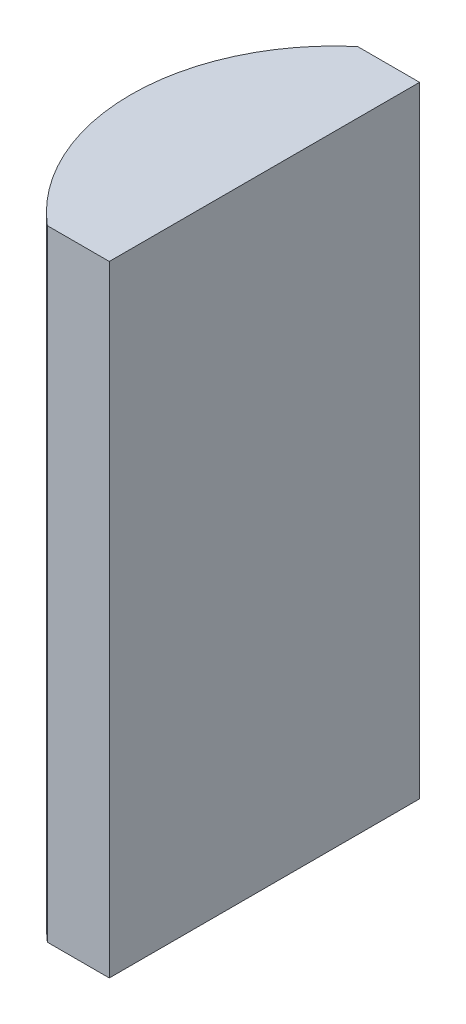
SolidWorks part; units mm, degrees
ref_plane "前视基准面" through (0, 0, 0) normal (0, 0, 1) x (1, 0, 0)
ref_plane "上视基准面" through (0, 0, 0) normal (0, 1, 0) x (1, 0, 0)
ref_plane "右视基准面" through (0, 0, 0) normal (1, 0, 0) x (0, 0, -1)
sketch "草图1" plane through (0, 0, 0) normal (0, 1, 0) x (1, 0, 0)
  line L0 (10.7432, 0) -> (-19.1624, 0) construction
  line L1 (0.1086, 5) -> (2.1052, 5)
  line L2 (0.1086, -5) -> (2.1052, -5)
  line L3 (2.1052, 5) -> (2.1052, -5)
  arc A0 (0.1086, 5) -> (0.1086, -5) centre (4.3552, 0) ccw
  point P19 (-2.2048, 0)
  point P20 (2.1052, 0)
  dimension "D2" = 5
  dimension "D3" = 6.56
  dimension "D4" = 4.31
  dimension "D1" = 5
extrude "凸台-拉伸1" add sketch "草图1" along normal blind 20
